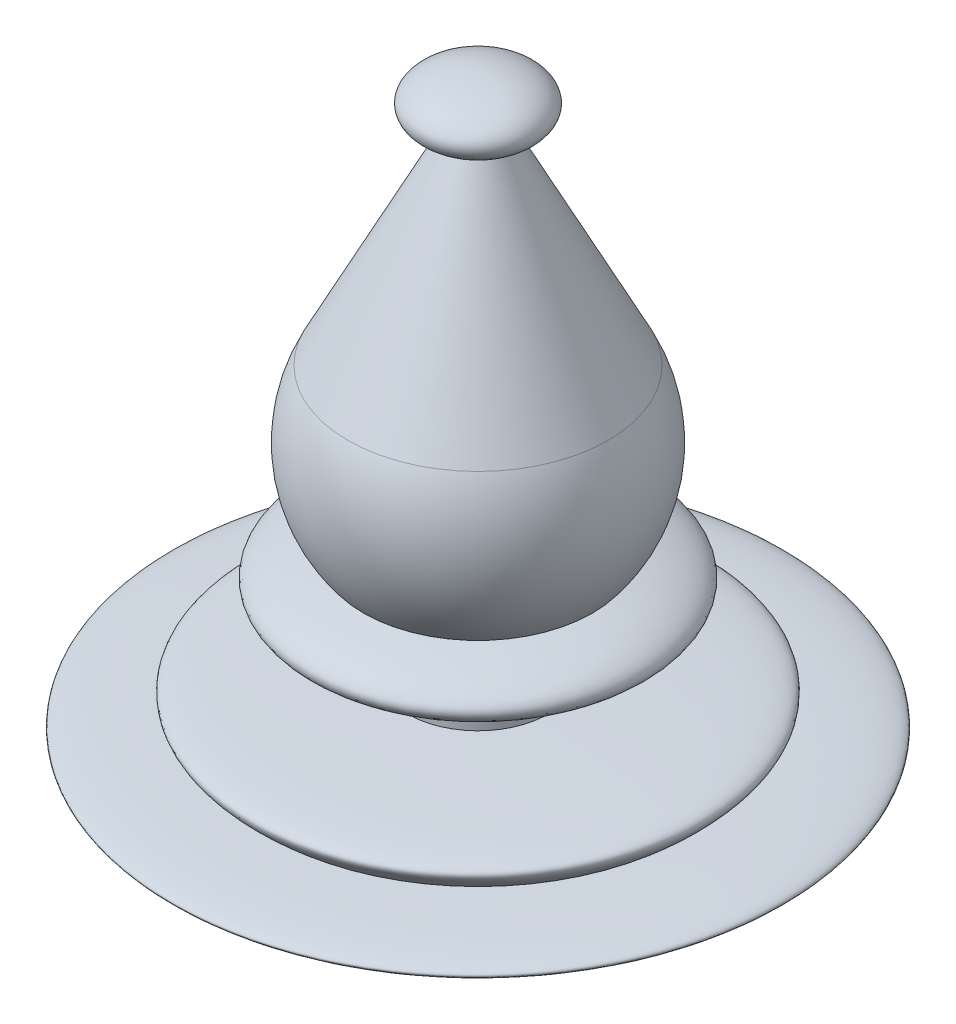
SolidWorks part; units mm, degrees
ref_plane "Front Plane" through (0, 0, 0) normal (0, 0, 1) x (1, 0, 0)
ref_plane "Top Plane" through (0, 0, 0) normal (0, 1, 0) x (1, 0, 0)
ref_plane "Right Plane" through (0, 0, 0) normal (1, 0, 0) x (0, 0, -1)
sketch "Sketch1" plane through (0, 0, 0) normal (0, 0, 1) x (1, 0, 0)
  line L0 (6, -12.8021) -> (6, -13)
  line L1 (2.2292, 22.9729) -> (11.9166, 4.0391)
  line L2 (0, 27.2617) -> (0, -72.7383)
  line L6 (6, -13) -> (6, -17.0494)
  arc A1 (9.7546, -7.7337) -> (11.0821, 5.6701) centre (0, 0) ccw
  ellipse E0 centre (0, 25) end of major axis (5.026, 25) minor radius 2.2617 (2.2292, 22.9729) -> (0, 27.2617) ccw
  ellipse E1 centre (0, -10) end of major axis (14.3875, -10) minor radius 3.083 (6, -12.8021) -> (9.7546, -7.7337) ccw
  ellipse E2 centre (0, -22.5494) end of major axis (25.9855, -21.0172) minor radius 2 (0, -24.5529) -> (18, -20.0494) ccw
  conic Q0 (6, -17.0494) -> (18, -20.0494) control (20.916, -17.5127) rho 0.73119
  point P12 (18, -20.0494)
  point P13 (0, 25)
  point P24 (0, -22.5494)
  dimension "D1" = 6
  dimension "D2" = 25
  dimension "D3" = 0
  dimension "D4" = 18
  dimension "D5" = 100
  dimension "D6" = 2.5
revolve "Revolve1" add sketch "Sketch1" angle 360 about L2
